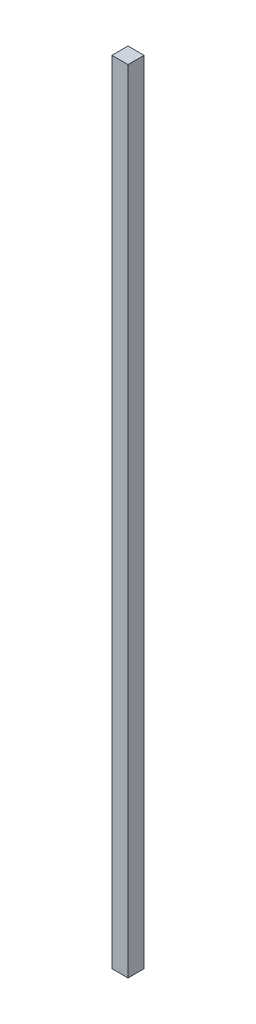
SolidWorks part; units mm, degrees
ref_plane "Спереди" through (0, 0, 0) normal (0, 0, 1) x (1, 0, 0)
ref_plane "Сверху" through (0, 0, 0) normal (0, 1, 0) x (1, 0, 0)
ref_plane "Справа" through (0, 0, 0) normal (1, 0, 0) x (0, 0, -1)
sketch "Эскиз1" plane through (0, 0, 0) normal (0, 1, 0) x (1, 0, 0)
  line L1 (-2.5, 2.5) -> (2.5, 2.5)
  line L2 (-2.5, 2.5) -> (-2.5, -2.5)
  line L3 (-2.5, -2.5) -> (2.5, -2.5)
  line L4 (2.5, 2.5) -> (2.5, -2.5)
  line L5 (-2.5, 2.5) -> (2.5, -2.5) construction
  line L6 (-2.5, -2.5) -> (2.5, 2.5) construction
  point P0 (0, 0)
extrude "Бобышка-Вытянуть1" add sketch "Эскиз1" along normal blind 245.2
sketch "Эскиз2" plane through (-2.5, 0, 0) normal (-1, 0, 0) x (0, 0, 1)
  line L0 (0, 245.2) -> (0, 0)
  line L1 (-2.5, 245.2) -> (2.5, 245.2) construction
  line L2 (-2.5, 0) -> (2.5, 0) construction
